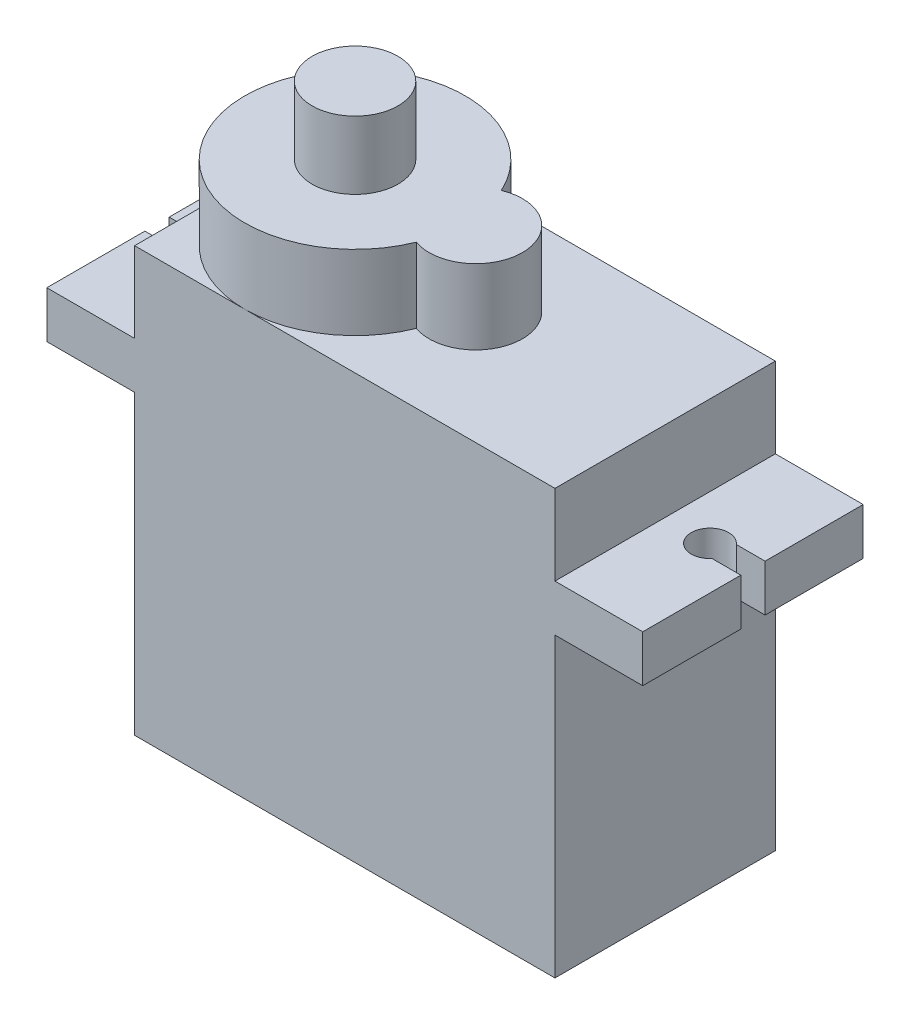
SolidWorks part; units mm, degrees
ref_plane "Plan de face" through (0, 0, 0) normal (0, 0, 1) x (1, 0, 0)
ref_plane "Plan de dessus" through (0, 0, 0) normal (0, 1, 0) x (1, 0, 0)
ref_plane "Plan de droite" through (0, 0, 0) normal (1, 0, 0) x (0, 0, -1)
sketch "Esquisse1" plane through (0, 0, 0) normal (0, 0, 1) x (1, 0, 0)
  line L0 (0, 0) -> (-22.5, 0)
  line L1 (-22.5, 0) -> (-22.5, 15.9)
  line L2 (-22.5, 15.9) -> (-27.2, 15.9)
  line L3 (-27.2, 15.9) -> (-27.2, 18.4)
  line L4 (-27.2, 18.4) -> (-22.5, 18.4)
  line L5 (-22.5, 18.4) -> (-22.5, 22.7)
  line L6 (-22.5, 22.7) -> (0, 22.7)
  line L7 (0, 22.7) -> (0, 18.4)
  line L8 (0, 18.4) -> (4.7, 18.4)
  line L9 (4.7, 18.4) -> (4.7, 15.9)
  line L10 (4.7, 15.9) -> (0, 15.9)
  line L11 (0, 15.9) -> (0, 0)
  line L12 (-22.5, 15.9) -> (0, 15.9) construction
  line L13 (0, 18.4) -> (-22.5, 18.4) construction
  line L14 (-22.5, 18.4) -> (-22.5, 15.9) construction
  line L15 (0, 15.9) -> (0, 18.4) construction
  dimension "D1" = 22.5
  dimension "D2" = 15.9
  dimension "D3" = 2.5
  dimension "D4" = 4.3
  dimension "D5" = 4.7
  dimension "D6" = 4.7
extrude "Boss.-Extru.1" add sketch "Esquisse1" along normal blind 11.8 contours L1 L2 L3 L4 L5 L6 L7 L8 L9 L10 L11 L0
sketch "Esquisse2" plane through (0, 22.7, 0) normal (0, 1, 0) x (1, 0, 0)
  line L0 (-22.5, -11.8) -> (-22.5, 0) construction
  line L1 (-22.5, -11.8) -> (0, -11.8) construction
  circle A1 centre (-16.6, -5.9) radius 5.9
  dimension "D1" = 11.8
  dimension "D2" = 5.9
  dimension "D3" = 5.9
sketch "Esquisse3" plane through (0, 22.7, 0) normal (0, 1, 0) x (1, 0, 0)
  line L0 (0, -11.8) -> (0, 0) construction
  circle A0 centre (-10.3, -5.7384) radius 2.5
  dimension "D1" = 5
  dimension "D2" = 10.3
extrude "Boss.-Extru.3" add sketch "Esquisse2" along normal blind 4 contours A1
extrude "Boss.-Extru.4" add sketch "Esquisse3" along normal blind 4 contours A0
sketch "Esquisse5" plane through (0, 26.7, 0) normal (0, 1, 0) x (1, 0, 0)
  circle A0 centre (-16.6, -5.9) radius 2.3
  arc A2 (-11.2448, -3.4238) -> (-11.1249, -8.0984) centre (-16.6, -5.9) ccw construction
  dimension "D1" = 4.6
  dimension "D2" = 0
extrude "Boss.-Extru.5" add sketch "Esquisse5" along normal blind 3.63 contours A0
sketch "Esquisse6" plane through (0, 18.4, 0) normal (0, 1, 0) x (1, 0, 0)
  line L0 (0, 0) -> (4.7, 0) construction
  line L1 (4.7, -11.8) -> (4.7, 0) construction
  line L2 (6.6619, -5.9) -> (6.6619, -5.25)
  line L3 (6.6619, -5.9) -> (6.6619, -6.55)
  line L11 (6.6619, -6.55) -> (3.1599, -6.55)
  line L12 (6.6619, -5.25) -> (3.1599, -5.25)
  line L13 (2.4, -5.9) -> (6.6619, -5.9) construction
  line L14 (0, -11.8) -> (-22.5, -11.8) construction
  line L15 (-11.25, -11.8) -> (-11.25, 0) construction
  line L16 (0, 0) -> (-22.5, 0) construction
  line L17 (-24.9, -5.9) -> (-29.1619, -5.9) construction
  line L18 (-29.1619, -5.25) -> (-25.6599, -5.25)
  line L19 (-29.1619, -6.55) -> (-25.6599, -6.55)
  line L20 (-29.1619, -5.9) -> (-29.1619, -6.55)
  line L21 (-29.1619, -5.9) -> (-29.1619, -5.25)
  circle A0 centre (2.4, -5.9) radius 1 construction
  arc A1 (3.1599, -6.55) -> (3.1599, -5.25) centre (2.4, -5.9) cw
  circle A2 centre (-24.9, -5.9) radius 1 construction
  arc A3 (-25.6599, -6.55) -> (-25.6599, -5.25) centre (-24.9, -5.9) ccw
  dimension "D1" = 2
  dimension "D2" = 5.9
  dimension "D3" = 2.3
  dimension "D4" = 0.65
  dimension "D5" = 0.65
  dimension "D6" = 3.502
extrude "Enlèv. mat.-Extru.7" cut sketch "Esquisse6" against normal up to next
sketch "Esquisse11" plane through (0, 30.33, 0) normal (0, 1, 0) x (1, 0, 0)
  line L0 (-16.6, -5.9) -> (-18.9, -5.9) construction
  circle A0 centre (-16.6, -5.9) radius 2.3 construction
sketch "Esquisse14" plane through (0, 26.7, 0) normal (0, 1, 0) x (1, 0, 0)
  line L0 (-16.6, -5.9) -> (-18.9, -5.9) construction
  line L1 (-16.6, -5.9) -> (-16.6, -8.2) construction
  circle A0 centre (-16.6, -5.9) radius 2.3 construction
sketch "Esquisse16" plane through (-22.5, 0, 0) normal (-1, 0, 0) x (0, 0, 1)
  line L0 (11.8, 0) -> (0, 0) construction
  line L5 (11.8, 0) -> (11.8, 15.9) construction
  line L6 (4.1, 0) -> (4.1, 4.5) construction
  line L7 (4.1, 4.5) -> (0, 4.5) construction
  line L8 (0, 0) -> (0, 15.9) construction
  line L9 (7.7, 5.7) -> (11.8, 5.7) construction
  line L11 (4.1, 4.5) -> (7.7, 4.5)
  line L12 (4.1, 4.5) -> (4.1, 5.7)
  line L13 (4.1, 5.7) -> (7.7, 5.7)
  line L14 (7.7, 4.5) -> (7.7, 5.7)
extrude "Boss.-Extru.8" add sketch "Esquisse16" along normal blind 1.2
move or copy body "Corps-Déplacer/Copier1" [suppressed] bodies to move or copy 108
